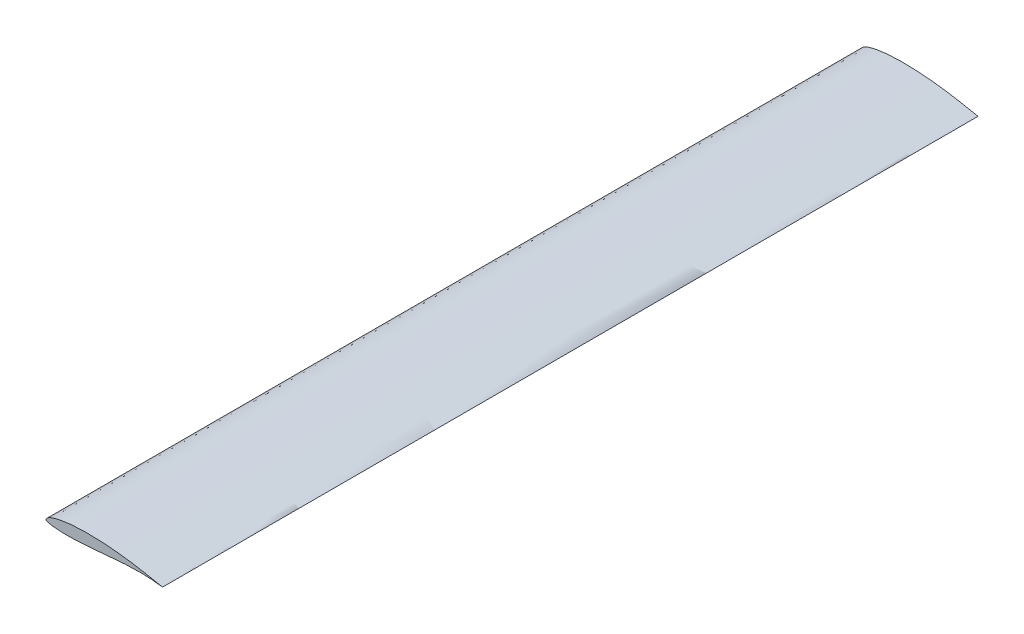
SolidWorks part; units mm, degrees
ref_plane "Front Plane" through (0, 0, 0) normal (0, 0, 1) x (1, 0, 0)
ref_plane "Top Plane" through (0, 0, 0) normal (0, 1, 0) x (1, 0, 0)
ref_plane "Right Plane" through (0, 0, 0) normal (1, 0, 0) x (0, 0, -1)
curve "Curve1"
  spline degree 3 poles (162.5054, 0.2399, 0) (164.3766, -0.0674, 0) (162.4984, 0.2974, 0) (160.9663, 0.6169, 0) (157.2301, 1.3585, 0) (152.6477, 2.2767, 0) (146.6748, 3.4526, 0) (139.6639, 4.7881, 0) (131.643, 6.2255, 0) (122.7797, 7.6781, 0) (113.2147, 9.0626, 0) (103.1148, 10.3087, 0) (92.6533, 11.3669, 0) (82.0087, 12.1836, 0) (71.3637, 12.7327, 0) (62.5731, 12.9388, 0) (55.6792, 12.9316, 0) (50.6638, 12.8397, 0) (45.7822, 12.6595, 0) (41.0552, 12.3904, 0) (36.5037, 12.0364, 0) (32.1469, 11.6018, 0) (28.0042, 11.0851, 0) (24.0917, 10.4983, 0) (20.4268, 9.8439, 0) (17.0258, 9.1308, 0) (13.9022, 8.3694, 0) (11.0683, 7.5656, 0) (8.5358, 6.7201, 0) (6.3124, 5.8329, 0) (4.4134, 4.8901, 0) (2.8451, 3.9032, 0) (1.6205, 2.9011, 0) (0.7312, 1.9381, 0) (0.1795, 1.0687, 0) (-0.0695, 0.2848, 0) (0.134, -0.4237, 0) (0.7641, -0.9032, 0) (1.6676, -1.285, 0) (2.8964, -1.6679, 0) (4.4544, -2.0608, 0) (6.3422, -2.4633, 0) (8.5547, -2.8492, 0) (11.0822, -3.197, 0) (13.9135, -3.4896, 0) (17.0355, -3.7334, 0) (20.4357, -3.9192, 0) (24.0994, -4.0549, 0) (28.0109, -4.1275, 0) (32.1529, -4.141, 0) (36.5088, -4.0825, 0) (41.0598, -3.9492, 0) (45.7863, -3.7367, 0) (50.6672, -3.4456, 0) (55.6815, -3.078, 0) (62.5754, -2.51, 0) (71.36, -1.6878, 0) (81.9977, -0.6546, 0) (92.6366, 0.3301, 0) (103.0952, 1.1742, 0) (113.1952, 1.8014, 0) (122.7632, 2.1758, 0) (131.6325, 2.2841, 0) (139.6597, 2.1473, 0) (146.6766, 1.8263, 0) (152.6515, 1.3776, 0) (157.2376, 0.925, 0) (160.9651, 0.442, 0) (162.5054, 0.2399, 0) (164.3766, -0.0674, 0) (162.4984, 0.2974, 0) knots -0.01889 -0.00847 -0.00213 0 0.002148 0.00855 0.019093 0.033602 0.051812 0.073403 0.097969 0.12507 0.15422 0.18491 0.21662 0.248811 0.280949 0.312507 0.327907 0.342969 0.357635 0.371852 0.385562 0.398705 0.41124 0.423118 0.434295 0.444729 0.454376 0.463215 0.471223 0.478387 0.484735 0.490273 0.49502 0.498937 0.502002 0.504262 0.5061 0.508218 0.511109 0.514949 0.519768 0.525568 0.532309 0.53997 0.548516 0.557914 0.568141 0.57915 0.590897 0.603335 0.616414 0.630088 0.644296 0.658978 0.674077 0.689528 0.721211 0.753454 0.785684 0.817334 0.84785 0.876721 0.903468 0.927655 0.94889 0.966808 0.98111 0.99153 0.99787 1 1.002148 1.00855 1.019093 periodic
sketch "Sketch2" plane through (0, 0, 0) normal (0, 0, 1) x (1, 0, 0)
  spline S0 degree 3 poles (162.5054, 0.2399) (164.3766, -0.0674) (162.4984, 0.2974) (160.9663, 0.6169) (157.2301, 1.3585) (152.6477, 2.2767) (146.6748, 3.4526) (139.6639, 4.7881) (131.643, 6.2255) (122.7797, 7.6781) (113.2147, 9.0626) (103.1148, 10.3087) (92.6533, 11.3669) (82.0087, 12.1836) (71.3637, 12.7327) (62.5731, 12.9388) (55.6792, 12.9316) (50.6638, 12.8397) (45.7822, 12.6595) (41.0552, 12.3904) (36.5037, 12.0364) (32.1469, 11.6018) (28.0042, 11.0851) (24.0917, 10.4983) (20.4268, 9.8439) (17.0258, 9.1308) (13.9022, 8.3694) (11.0683, 7.5656) (8.5358, 6.7201) (6.3124, 5.8329) (4.4134, 4.8901) (2.8451, 3.9032) (1.6205, 2.9011) (0.7312, 1.9381) (0.1795, 1.0687) (-0.0695, 0.2848) (0.134, -0.4237) (0.7641, -0.9032) (1.6676, -1.285) (2.8964, -1.6679) (4.4544, -2.0608) (6.3422, -2.4633) (8.5547, -2.8492) (11.0822, -3.197) (13.9135, -3.4896) (17.0355, -3.7334) (20.4357, -3.9192) (24.0994, -4.0549) (28.0109, -4.1275) (32.1529, -4.141) (36.5088, -4.0825) (41.0598, -3.9492) (45.7863, -3.7367) (50.6672, -3.4456) (55.6815, -3.078) (62.5754, -2.51) (71.36, -1.6878) (81.9977, -0.6546) (92.6366, 0.3301) (103.0952, 1.1742) (113.1952, 1.8014) (122.7632, 2.1758) (131.6325, 2.2841) (139.6597, 2.1473) (146.6766, 1.8263) (152.6515, 1.3776) (157.2376, 0.925) (160.9651, 0.442) (162.5054, 0.2399) (164.3766, -0.0674) (162.4984, 0.2974) knots -0.01889 -0.00847 -0.00213 0 0.002148 0.00855 0.019093 0.033602 0.051812 0.073403 0.097969 0.12507 0.15422 0.18491 0.21662 0.248811 0.280949 0.312507 0.327907 0.342969 0.357635 0.371852 0.385562 0.398705 0.41124 0.423118 0.434295 0.444729 0.454376 0.463215 0.471223 0.478387 0.484735 0.490273 0.49502 0.498937 0.502002 0.504262 0.5061 0.508218 0.511109 0.514949 0.519768 0.525568 0.532309 0.53997 0.548516 0.557914 0.568141 0.57915 0.590897 0.603335 0.616414 0.630088 0.644296 0.658978 0.674077 0.689528 0.721211 0.753454 0.785684 0.817334 0.84785 0.876721 0.903468 0.927655 0.94889 0.966808 0.98111 0.99153 0.99787 1 1.002148 1.00855 1.019093 only from (164, 0) to (164, 0) construction
  spline S1 degree 3 poles (162.5054, 0.2399) (164.3766, -0.0674) (162.4984, 0.2974) (160.9663, 0.6169) (157.2301, 1.3585) (152.6477, 2.2767) (146.6748, 3.4526) (139.6639, 4.7881) (131.643, 6.2255) (122.7797, 7.6781) (113.2147, 9.0626) (103.1148, 10.3087) (92.6533, 11.3669) (82.0087, 12.1836) (71.3637, 12.7327) (62.5731, 12.9388) (55.6792, 12.9316) (50.6638, 12.8397) (45.7822, 12.6595) (41.0552, 12.3904) (36.5037, 12.0364) (32.1469, 11.6018) (28.0042, 11.0851) (24.0917, 10.4983) (20.4268, 9.8439) (17.0258, 9.1308) (13.9022, 8.3694) (11.0683, 7.5656) (8.5358, 6.7201) (6.3124, 5.8329) (4.4134, 4.8901) (2.8451, 3.9032) (1.6205, 2.9011) (0.7312, 1.9381) (0.1795, 1.0687) (-0.0695, 0.2848) (0.134, -0.4237) (0.7641, -0.9032) (1.6676, -1.285) (2.8964, -1.6679) (4.4544, -2.0608) (6.3422, -2.4633) (8.5547, -2.8492) (11.0822, -3.197) (13.9135, -3.4896) (17.0355, -3.7334) (20.4357, -3.9192) (24.0994, -4.0549) (28.0109, -4.1275) (32.1529, -4.141) (36.5088, -4.0825) (41.0598, -3.9492) (45.7863, -3.7367) (50.6672, -3.4456) (55.6815, -3.078) (62.5754, -2.51) (71.36, -1.6878) (81.9977, -0.6546) (92.6366, 0.3301) (103.0952, 1.1742) (113.1952, 1.8014) (122.7632, 2.1758) (131.6325, 2.2841) (139.6597, 2.1473) (146.6766, 1.8263) (152.6515, 1.3776) (157.2376, 0.925) (160.9651, 0.442) (162.5054, 0.2399) (164.3766, -0.0674) (162.4984, 0.2974) knots -0.01889 -0.00847 -0.00213 0 0.002148 0.00855 0.019093 0.033602 0.051812 0.073403 0.097969 0.12507 0.15422 0.18491 0.21662 0.248811 0.280949 0.312507 0.327907 0.342969 0.357635 0.371852 0.385562 0.398705 0.41124 0.423118 0.434295 0.444729 0.454376 0.463215 0.471223 0.478387 0.484735 0.490273 0.49502 0.498937 0.502002 0.504262 0.5061 0.508218 0.511109 0.514949 0.519768 0.525568 0.532309 0.53997 0.548516 0.557914 0.568141 0.57915 0.590897 0.603335 0.616414 0.630088 0.644296 0.658978 0.674077 0.689528 0.721211 0.753454 0.785684 0.817334 0.84785 0.876721 0.903468 0.927655 0.94889 0.966808 0.98111 0.99153 0.99787 1 1.002148 1.00855 1.019093 only from (164, 0) to (164, 0)
extrude "Boss-Extrude1" add sketch "Sketch2" along normal blind 1147.5
sketch "Sketch3" plane through (0, 0, 1147.5) normal (0, 0, 1) x (1, 0, 0)
  line L0 (0, 0) -> (164, 0) construction
  spline S0 degree 3 poles (162.5054, 0.2399) (164.3766, -0.0674) (162.4984, 0.2974) (160.9663, 0.6169) (157.2301, 1.3585) (152.6477, 2.2767) (146.6748, 3.4526) (139.6639, 4.7881) (131.643, 6.2255) (122.7797, 7.6781) (113.2147, 9.0626) (103.1148, 10.3087) (92.6533, 11.3669) (82.0087, 12.1836) (71.3637, 12.7327) (62.5731, 12.9388) (55.6792, 12.9316) (50.6638, 12.8397) (45.7822, 12.6595) (41.0552, 12.3904) (36.5037, 12.0364) (32.1469, 11.6018) (28.0042, 11.0851) (24.0917, 10.4983) (20.4268, 9.8439) (17.0258, 9.1308) (13.9022, 8.3694) (11.0683, 7.5656) (8.5358, 6.7201) (6.3124, 5.8329) (4.4134, 4.8901) (2.8451, 3.9032) (1.6205, 2.9011) (0.7312, 1.9381) (0.1795, 1.0687) (-0.0695, 0.2848) (0.134, -0.4237) (0.7641, -0.9032) (1.6676, -1.285) (2.8964, -1.6679) (4.4544, -2.0608) (6.3422, -2.4633) (8.5547, -2.8492) (11.0822, -3.197) (13.9135, -3.4896) (17.0355, -3.7334) (20.4357, -3.9192) (24.0994, -4.0549) (28.0109, -4.1275) (32.1529, -4.141) (36.5088, -4.0825) (41.0598, -3.9492) (45.7863, -3.7367) (50.6672, -3.4456) (55.6815, -3.078) (62.5754, -2.51) (71.36, -1.6878) (81.9977, -0.6546) (92.6366, 0.3301) (103.0952, 1.1742) (113.1952, 1.8014) (122.7632, 2.1758) (131.6325, 2.2841) (139.6597, 2.1473) (146.6766, 1.8263) (152.6515, 1.3776) (157.2376, 0.925) (160.9651, 0.442) (162.5054, 0.2399) (164.3766, -0.0674) (162.4984, 0.2974) knots -0.01889 -0.00847 -0.00213 0 0.002148 0.00855 0.019093 0.033602 0.051812 0.073403 0.097969 0.12507 0.15422 0.18491 0.21662 0.248811 0.280949 0.312507 0.327907 0.342969 0.357635 0.371852 0.385562 0.398705 0.41124 0.423118 0.434295 0.444729 0.454376 0.463215 0.471223 0.478387 0.484735 0.490273 0.49502 0.498937 0.502002 0.504262 0.5061 0.508218 0.511109 0.514949 0.519768 0.525568 0.532309 0.53997 0.548516 0.557914 0.568141 0.57915 0.590897 0.603335 0.616414 0.630088 0.644296 0.658978 0.674077 0.689528 0.721211 0.753454 0.785684 0.817334 0.84785 0.876721 0.903468 0.927655 0.94889 0.966808 0.98111 0.99153 0.99787 1 1.002148 1.00855 1.019093 only from (164, 0) to (164, 0) construction
